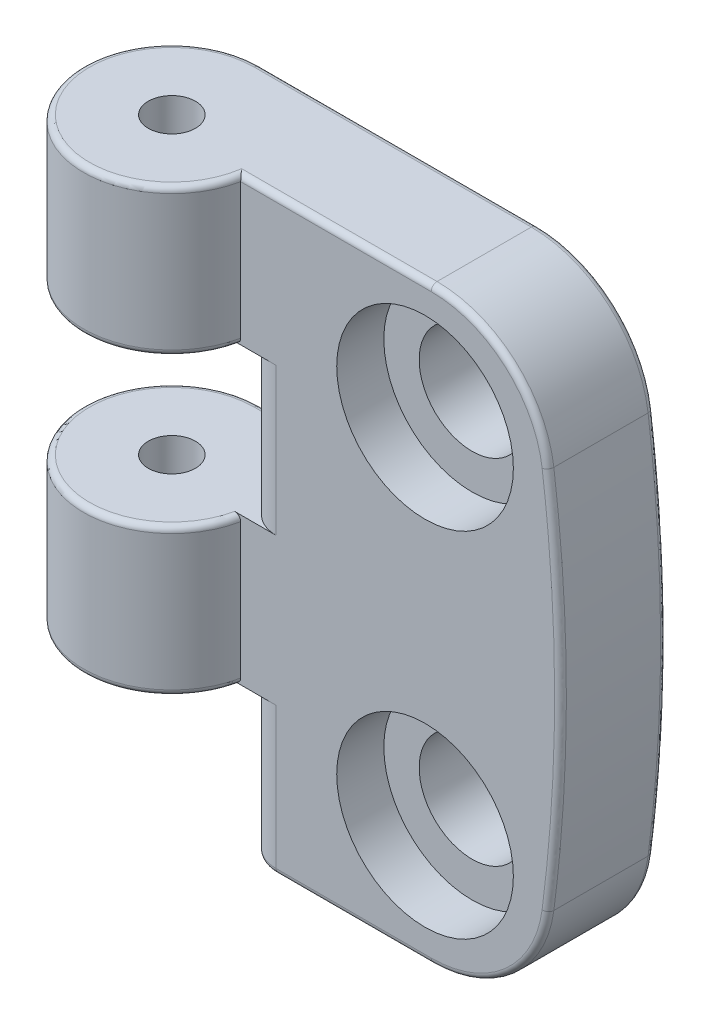
SolidWorks part; units mm, degrees
material "POM Acetal Copolymer"
ref_plane "Plan de face" through (0, 0, 0) normal (0, 0, 1) x (1, 0, 0)
ref_plane "Plan de dessus" through (0, 0, 0) normal (0, 1, 0) x (1, 0, 0)
ref_plane "Plan de droite" through (0, 0, 0) normal (1, 0, 0) x (0, 0, -1)
sketch "Sketch1" plane through (0, 0, 0) normal (0, 0, 1) x (1, 0, 0)
  line L1 (0, 0) -> (42, 0)
  line L2 (0, 0) -> (0, 50)
  line L3 (0, 50) -> (42, 50)
  line L4 (42, 0) -> (42, 50)
  dimension "D1" = 42
  dimension "D2" = 50
extrude "Boss-Extrude1" add sketch "Sketch1" along normal blind 15
sketch "Sketch2" plane through (0, 0, 0) normal (0, -1, 0) x (1, 0, 0)
  line L0 (0, 15) -> (0, 0) construction
  line L2 (42, 0) -> (7.5, 0)
  line L3 (42, 0) -> (42, 9)
  line L4 (42, 9) -> (14.8485, 9)
  arc A0 (14.8485, 9) -> (7.5, 0) centre (7.5, 7.5) ccw
  circle A1 centre (7.5, 7.5) radius 2
  dimension "D1" = 9
  dimension "D2" = 4
extrude "Cut-Extrude1" cut sketch "Sketch2" against normal through all flip side to cut
sketch "Sketch3" plane through (0, 0, 9) normal (0, 0, 1) x (1, 0, 0)
  line L0 (42, 50) -> (14.8485, 50) construction
  line L1 (42, 50) -> (42, 0) construction
  line L2 (42, 0) -> (14.8485, 0) construction
  line L4 (39.4975, 50) -> (57.0348, 50)
  line L6 (39.4975, 0) -> (57.0348, 0)
  line L7 (57.0348, 50) -> (57.0348, 0)
  spline S0 degree 2 poles (39.4975, 50) (44.5025, 25) (39.4975, 0) knots 0 0 0 1 1 1
  point P2 (39.4975, 0)
extrude "Cut-Extrude2" cut sketch "Sketch3" against normal blind 15
fillet "Fillet1" radius 10 2 edges at (39.4975, 50, 4.5) (39.4975, 0, 4.5)
hole_wizard "CBORE for M8 Hex Socket Head Cap Screw1" positions "Sketch4" profile "Sketch5" counterbore size "M8" standard "ISO"
sketch "Sketch4" plane through (0, 0, 9) normal (0, 0, 1) x (1, 0, 0)
  line L0 (31.021, 50) -> (14.8485, 50) construction
  line L2 (14.8485, 50) -> (14.8485, 0) construction
  point P0 (30.4985, 10)
  point P2 (30.4985, 40)
  point P9 (28.4688, 40)
  dimension "D1" = 30
  dimension "D2" = 10
  dimension "D3" = 15.65
sketch "Sketch5" plane through (30.4985, 10, 9) normal (1, 0, 0) x (0, -1, 0)
  line L0 (0, 0) -> (0, 17.7039)
  line L1 (0, 17.7039) -> (4.5, 15)
  line L2 (4.5, 15) -> (4.5, 4)
  line L3 (4.5, 4) -> (7.5, 4)
  line L4 (7.5, 4) -> (7.5, 0)
  line L5 (7.5, 0) -> (0, 0)
  line L10 (0, 17.7039) -> (-4.5, 15) construction
  line L11 (0, -6.35) -> (0, 107.95) construction
  dimension "Hole Dia." = 9
  dimension "Hole Depth" = 15
  dimension "C'Bore Dia." = 15
  dimension "C'Bore Depth" = 4
  dimension "Drill Angle" = 118
sketch "Sketch6" plane through (0, 0, 9) normal (0, 0, 1) x (1, 0, 0)
  line L0 (14.8485, 50) -> (14.8485, 0) construction
  line L1 (0, 0) -> (14.8485, 0)
  line L2 (0, 0) -> (0, 12.5)
  line L3 (0, 12.5) -> (14.8485, 12.5)
  line L4 (14.8485, 0) -> (14.8485, 12.5)
  line L5 (0, 50) -> (0, 0) construction
  line L6 (0, 25) -> (14.8485, 25)
  line L7 (0, 25) -> (0, 37.5)
  line L8 (0, 37.5) -> (14.8485, 37.5)
  line L9 (14.8485, 25) -> (14.8485, 37.5)
  dimension "D1" = 12.5
  dimension "D2" = 12.5
  dimension "D3" = 12.5
extrude "Cut-Extrude3" cut sketch "Sketch6" against normal through all both and the other way through all
fillet "Fillet2" radius 3 4 edges at (14.8485, 31.25, 0) (14.8485, 31.25, 9) (14.8485, 6.25, 0) (14.8485, 6.25, 9)
fillet "Fillet3" radius 0.5 20 edges at (12.6742, 25, 0) (12.6742, 12.5, 0) (22.9348, 50, 9) (37.6188, 47.5146, 9) (37.6188, 2.4854, 9) (24.4348, 0, 9) (15.7271, 0, 8.1213) (14.8485, 0, 4.5) (15.7271, 0, 0.8787) (24.4348, 0, 0) (37.6188, 2.4854, 0) (37.6188, 47.5146, 0) (19.2605, 50, 0) (12.6742, 37.5, 0) (1.6905, 25, 12.2434) (1.6905, 12.5, 12.2434) (1.6905, 50, 12.2434) (1.6905, 37.5, 12.2434)
